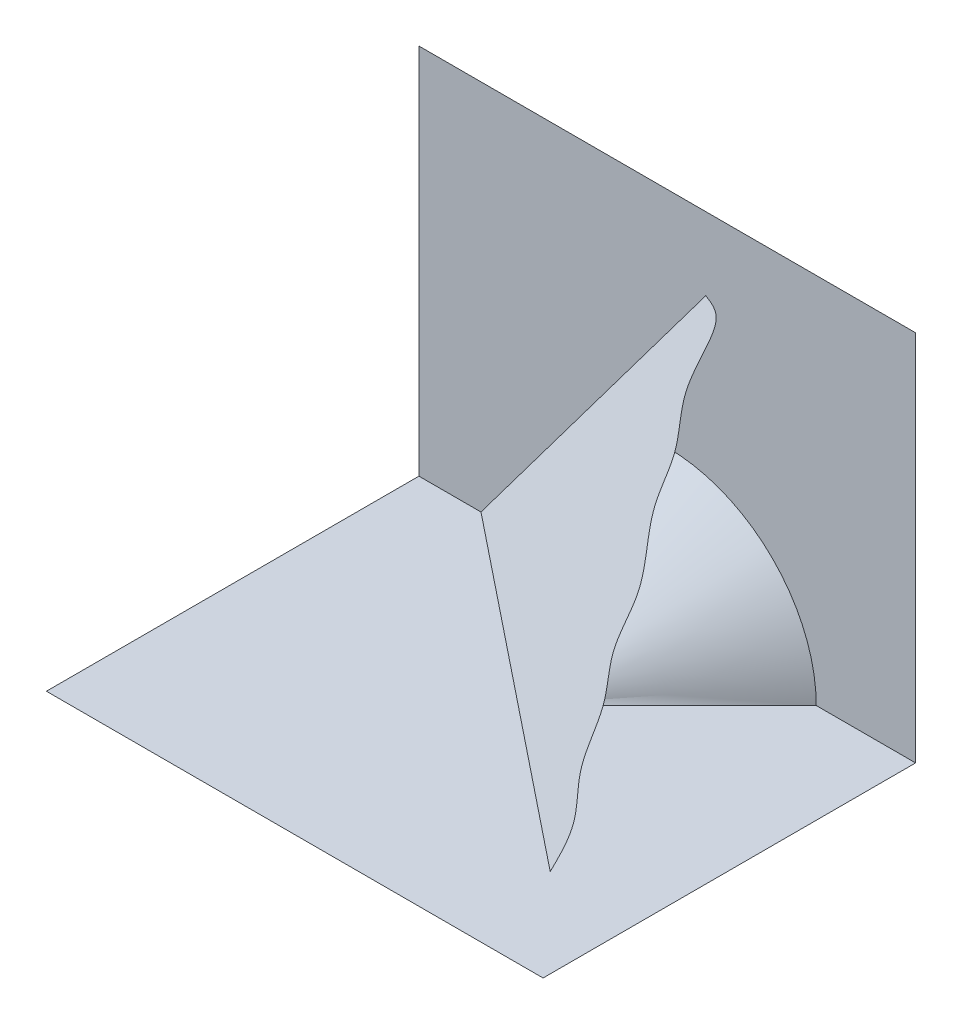
SolidWorks part; units mm, degrees
ref_plane "Front Plane" through (0, 0, 0) normal (0, 0, 1) x (1, 0, 0)
ref_plane "Top Plane" through (0, 0, 0) normal (0, 1, 0) x (1, 0, 0)
ref_plane "Right Plane" through (0, 0, 0) normal (1, 0, 0) x (0, 0, -1)
sketch "Sketch1" plane through (0, 0, 0) normal (0, 0, 1) x (1, 0, 0)
  line L1 (-100, 150) -> (100, 150)
  line L2 (-100, 150) -> (-100, 0)
  line L3 (-100, 0) -> (100, 0)
  line L4 (100, 150) -> (100, 0)
  dimension "D1" = 150
  dimension "D2" = 200
extrude "Extrude1" add sketch "Sketch1" against normal blind 0.0001
sketch "Sketch2" plane through (0, 0, 0) normal (0, 1, 0) x (1, 0, 0)
  line L1 (-100, 0) -> (100, 0)
  line L2 (-100, 0) -> (-100, -150)
  line L3 (-100, -150) -> (100, -150)
  line L4 (100, 0) -> (100, -150)
  dimension "D1" = 200
  dimension "D2" = 150
extrude "Extrude2" add sketch "Sketch2" against normal blind 0.0001
sketch "Sketch3" plane through (0, 0, 0) normal (0, 1, 0) x (-1, 0, 0)
  line L0 (60, 0) -> (0, 60)
  line L1 (-100, 0) -> (100, 0) construction
  line L2 (0, 60) -> (0, 0) construction
  line L3 (-100, 0) -> (100, 0) construction
  line L4 (60, 0) -> (0, 0)
  line L5 (0, 60) -> (0, 0)
  dimension "D1" = 45
  dimension "D2" = 60
revolve "Revolve2" add sketch "Sketch3" angle 180 about L2
sketch "Sketch4" plane through (0, 0, 0) normal (0, 0, 1) x (1, 0, 0)
  line L0 (15.499, 120.6653) -> (-75, 0)
  line L1 (100, 0) -> (-100, 0) construction
  arc A0 (60, 0) -> (-60, 0) centre (0, 0) ccw construction
  dimension "D1" = 25
sketch "Sketch5" plane through (0, 0, 0) normal (0, 1, 0) x (-1, 0, 0)
  line L0 (75, 0) -> (-64.3524, 111.4819)
sketch3d "3DSketch1"
  line L0 (15.499, 120.6653, 0) -> (64.3524, 0, 111.4819)
surface "Surface-Fill1"
sketch "Sketch6" plane through (-24, 18, 30) normal (0.5657, -0.4243, -0.7071) x (-0.8246, -0.291, -0.4851)
  spline S0 degree 3 poles (-47.8995, 103.4696) (-55.2726, 103.4825) (-71.8254, 103.5112) (-55.8593, 76.9245) (-76.7598, 65.0734) (-69.7978, 41.7072) (-94.3308, 28.3402) (-82.758, 4.5702) (-100.6953, -8.0172) (-93.9353, -28.8443) (-114.5324, -39.4407) (-109.5802, -51.4478) (-107.143, -57.357) knots 0 0 0 0 0.090499 0.203174 0.305672 0.388577 0.531406 0.632577 0.716193 0.82018 0.911503 1 1 1 1
surface "Surface-Fill2"
surface "Surface-Knit1"
